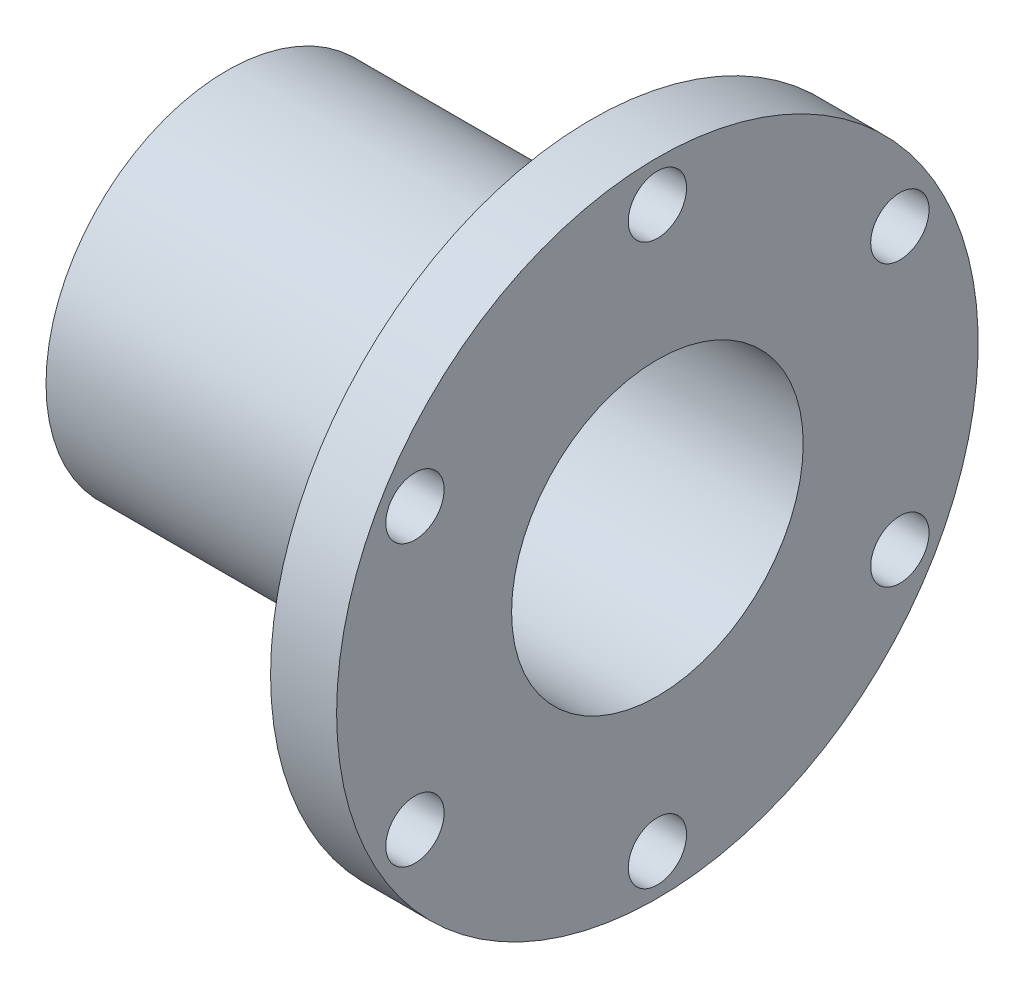
SolidWorks part; units mm, degrees
ref_plane "Front Plane" through (0, 0, 0) normal (0, 0, 1) x (1, 0, 0)
ref_plane "Top Plane" through (0, 0, 0) normal (0, 1, 0) x (1, 0, 0)
ref_plane "Right Plane" through (0, 0, 0) normal (1, 0, 0) x (0, 0, -1)
sketch "Sketch1" plane through (0, 0, 0) normal (0, 0, 1) x (1, 0, 0)
  line L0 (-203.3632, 0) -> (148.2063, 0) construction
  line L1 (-147.6457, 50) -> (0, 50)
  line L2 (0, 50) -> (0, 110)
  line L3 (0, 110) -> (-22.6457, 110)
  line L4 (-22.6457, 110) -> (-22.6457, 62)
  line L5 (-22.6457, 62) -> (-147.6457, 62)
  line L6 (-147.6457, 62) -> (-147.6457, 50)
  dimension "D1" = 50
  dimension "D2" = 62
  dimension "D3" = 110
  dimension "D4" = 22.6457
  dimension "D5" = 125
revolve "Revolve1" add sketch "Sketch1" angle 360 about L0
sketch "Sketch2" plane through (0, 0, 0) normal (1, 0, 0) x (0, 0, -1)
  line L0 (0, 143.2516) -> (0, -153.2615) construction
  circle A0 centre (0, 96) radius 10
  circle A1 centre (0, 0) radius 110 construction
  dimension "D2" = 20
  dimension "D1" = 96
extrude "Cut-Extrude1" cut sketch "Sketch2" against normal blind 30
pattern_circular "CirPattern1" count 6 over 360 about axis through (0, 0, 0) along (1, 0, 0) of "Cut-Extrude1"
